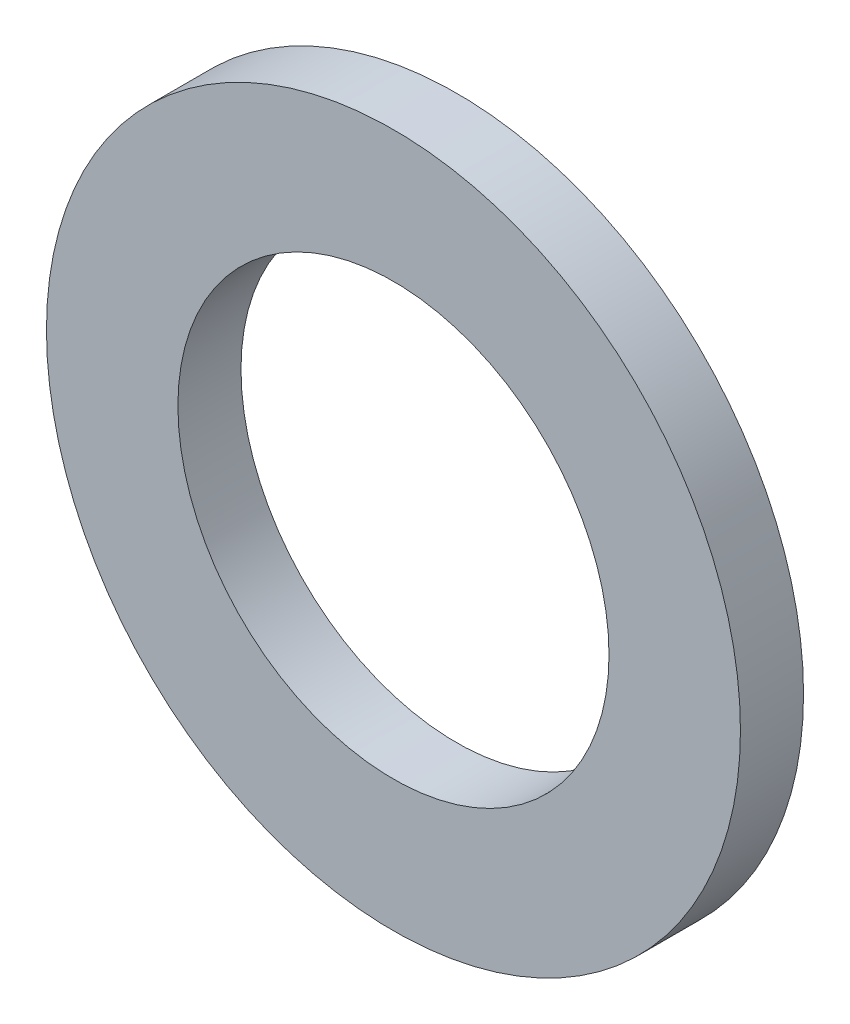
SolidWorks part; units mm, degrees
material "Сталь"
ref_plane "Спереди" through (0, 0, 0) normal (0, 0, 1) x (1, 0, 0)
ref_plane "Сверху" through (0, 0, 0) normal (0, 1, 0) x (1, 0, 0)
ref_plane "Справа" through (0, 0, 0) normal (1, 0, 0) x (0, 0, -1)
sketch "Эскиз1" plane through (0, 0, 0) normal (0, 0, 1) x (1, 0, 0)
  circle A0 centre (0, 0) radius 4.1
  circle A1 centre (0, 0) radius 6.6
  dimension "D1" = 8.2
  dimension "D2" = 2.5
extrude "Бобышка-Вытянуть1" add sketch "Эскиз1" along normal blind 1.2
